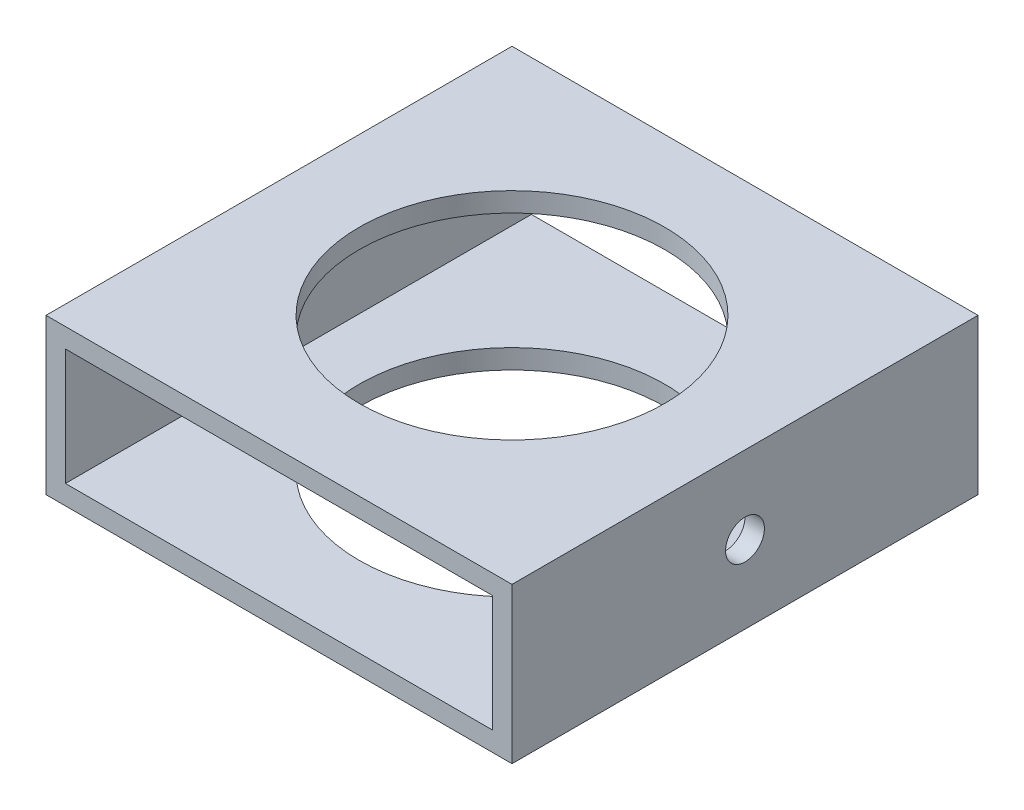
SolidWorks part; units mm, degrees
ref_plane "Front" through (0, 0, 0) normal (0, 0, 1) x (1, 0, 0)
ref_plane "Top" through (0, 0, 0) normal (0, 1, 0) x (1, 0, 0)
ref_plane "Right" through (0, 0, 0) normal (1, 0, 0) x (0, 0, -1)
sketch "Sketch1" plane through (0, 0, 0) normal (0, 0, 1) x (1, 0, 0)
  line L1 (-38.1, -12.7) -> (38.1, -12.7)
  line L2 (-38.1, -12.7) -> (-38.1, 12.7)
  line L3 (-38.1, 12.7) -> (38.1, 12.7)
  line L4 (38.1, -12.7) -> (38.1, 12.7)
  line L5 (-38.1, -12.7) -> (38.1, 12.7) construction
  line L6 (-38.1, 12.7) -> (38.1, -12.7) construction
  point P0 (0, 0)
  dimension "D1" = 25.4
  dimension "D2" = 76.2
extrude "Extrude-Thin1" add sketch "Sketch1" along normal mid plane 76.2 thin thin type one direction reverse wall 3.175
sketch "Sketch2" plane through (-38.1, 0, 0) normal (-1, 0, 0) x (0, 0, 1)
  circle A0 centre (0, 0) radius 3.175
  dimension "D1" = 6.35
extrude "Cut-Extrude1" cut sketch "Sketch2" against normal through all
sketch "Sketch3" plane through (0, 12.7, 0) normal (0, 1, 0) x (1, 0, 0)
  circle A0 centre (0, 0) radius 24.972
  dimension "D1" = 49.944
extrude "Cut-Extrude2" cut sketch "Sketch3" against normal through all
